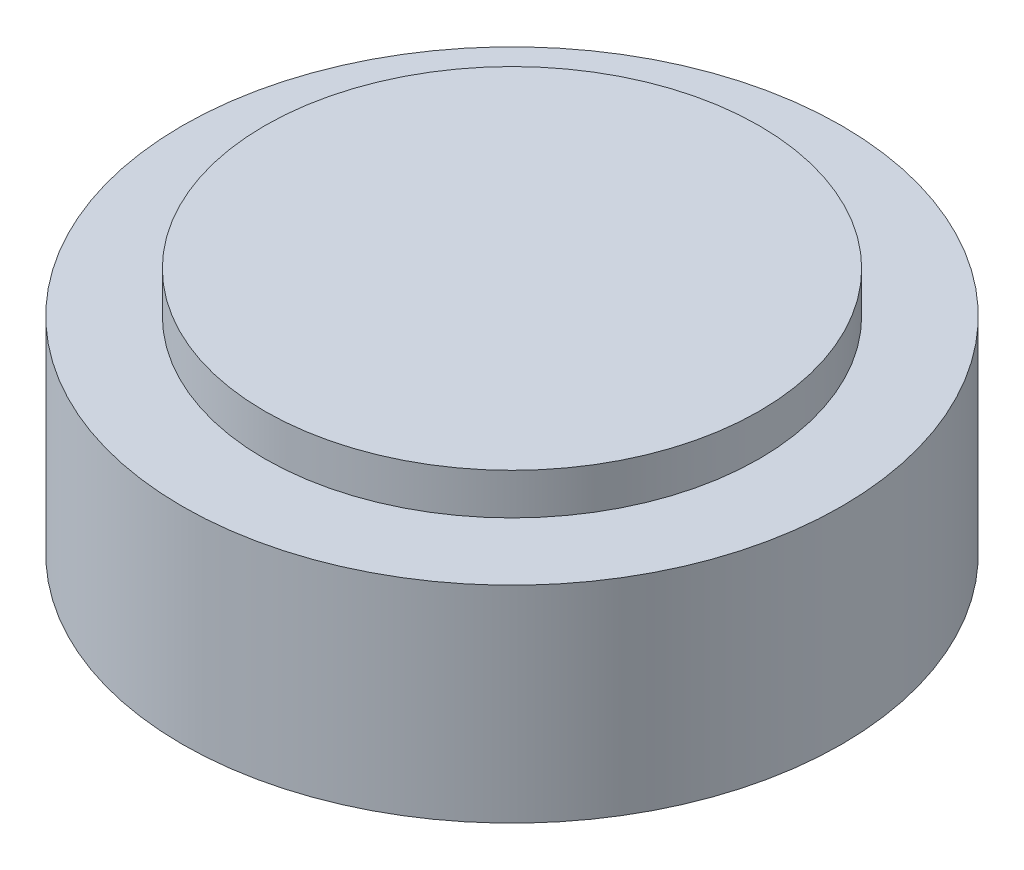
SolidWorks part; units mm, degrees
ref_plane "Front Plane" through (0, 0, 0) normal (0, 0, 1) x (1, 0, 0)
ref_plane "Top Plane" through (0, 0, 0) normal (0, 1, 0) x (1, 0, 0)
ref_plane "Right Plane" through (0, 0, 0) normal (1, 0, 0) x (0, 0, -1)
sketch "Sketch1" plane through (0, 0, 0) normal (0, 0, 1) x (1, 0, 0)
  line L0 (0, 0) -> (0, 30)
  line L1 (0, 30) -> (30, 30)
  line L2 (30, 30) -> (30, 25)
  line L3 (30, 25) -> (40, 25)
  line L4 (40, 25) -> (40, 0)
  line L5 (40, 0) -> (0, 0)
  line L6 (0, 0) -> (0, 30.5417) construction
  dimension "D1" = 5
  dimension "D2" = 80
  dimension "D3" = 10
  dimension "D4" = 30
revolve "Revolve1" add sketch "Sketch1" angle 360 about L6
sketch "Sketch2" plane through (0, 0, 0) normal (0, -1, 0) x (1, 0, 0)
  circle A0 centre (0, 0) radius 14
  dimension "D1" = 28
extrude "Cut-Extrude1" cut sketch "Sketch2" against normal blind 17
